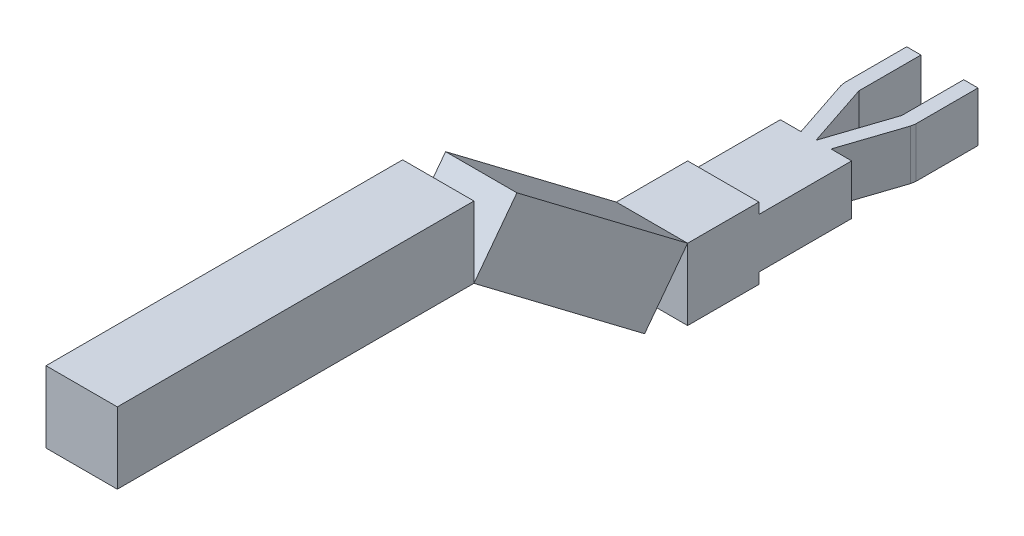
SolidWorks part; units mm, degrees
ref_plane "Front Plane" through (0, 0, 0) normal (0, 0, 1) x (1, 0, 0)
ref_plane "Top Plane" through (0, 0, 0) normal (0, 1, 0) x (1, 0, 0)
ref_plane "Right Plane" through (0, 0, 0) normal (1, 0, 0) x (0, 0, -1)
sketch "Sketch1" plane through (0, 0, 0) normal (0, 1, 0) x (1, 0, 0)
  line L0 (0, -105.7688) -> (-30, -15.63)
  line L1 (-50, 71.37) -> (-30, 71.37)
  line L2 (-50, 71.37) -> (-50, -15.63)
  line L4 (-30, 71.37) -> (-30, -15.63)
  line L5 (30, 71.37) -> (50, 71.37)
  line L6 (30, 71.37) -> (30, -15.63)
  line L8 (50, 71.37) -> (50, -15.63)
  line L9 (21.0786, -105.7688) -> (50, -105.7688)
  line L11 (-21.0786, -105.7688) -> (-48.9766, -21.9458)
  line L12 (0, -105.7688) -> (30, -15.63)
  line L13 (-48.9766, -21.9458) -> (-50, -15.63)
  line L15 (21.0786, -105.7688) -> (48.9766, -21.9458)
  line L16 (-30, 0) -> (0, 0) construction
  line L17 (0, 0) -> (30, 0) construction
  line L18 (50, -15.63) -> (48.9766, -21.9458)
  line L19 (-50, -105.7688) -> (-21.0786, -105.7688)
  line L20 (-50, -105.7688) -> (-50, -235.7688)
  line L21 (-50, -235.7688) -> (50, -235.7688)
  line L22 (50, -105.7688) -> (50, -235.7688)
  dimension "D1" = 20
  dimension "D2" = 20
  dimension "D3" = 60
  dimension "D4" = 87
  dimension "D5" = 95
  dimension "D6" = 100
  dimension "D7" = 130
  dimension "D8" = 20
  dimension "D9" = 20
extrude "Boss-Extrude1" add sketch "Sketch1" along normal blind 70
sketch "Sketch2" plane through (0, 0, 235.7688) normal (0, 0, 1) x (1, 0, 0)
  line L0 (0, 70) -> (0, 0) construction
  line L1 (50, 85) -> (-50, 85)
  line L2 (50, 85) -> (50, -15)
  line L3 (50, -15) -> (-50, -15)
  line L4 (-50, 85) -> (-50, -15)
  line L5 (-50, 70) -> (50, 70) construction
  line L6 (-50, 0) -> (50, 0) construction
  line L7 (0, 0) -> (50, 35) construction
  line L8 (50, 70) -> (50, 0) construction
  line L9 (50, 35) -> (-50, 35) construction
  line L10 (-50, 70) -> (-50, 0) construction
  line L11 (50, 70) -> (0, 35) construction
  line L12 (0, 35) -> (-50, 0) construction
  line L13 (0, 85) -> (0, -15) construction
  point P23 (0, 35)
  dimension "D1" = 100
  dimension "D2" = 100
extrude "Boss-Extrude2" add sketch "Sketch2" along normal blind 100
sketch "Sketch3" plane through (-50, 0, 0) normal (-1, 0, 0) x (0, 0, 1)
  line L0 (335.7688, 85) -> (396.0621, 5.2208)
  line L1 (335.7688, 85) -> (575.1064, 265.8799)
  line L2 (396.0621, 5.2208) -> (635.3996, 186.1007)
  line L3 (575.1064, 265.8799) -> (635.3996, 186.1007)
  dimension "D1" = 100
  dimension "D2" = 300
extrude "Boss-Extrude3" add sketch "Sketch3" against normal blind 100 separate body
sketch "Sketch4" plane through (-50, 0, 0) normal (-1, 0, 0) x (0, 0, 1)
  line L0 (635.3996, 186.1007) -> (1135.3996, 186.1007)
  line L1 (635.3996, 186.1007) -> (635.3996, 286.1007)
  line L2 (1135.3996, 186.1007) -> (1135.3996, 286.1007)
  line L3 (635.3996, 286.1007) -> (1135.3996, 286.1007)
  dimension "D1" = 100
  dimension "D2" = 500
extrude "Boss-Extrude4" add sketch "Sketch4" against normal blind 100 separate body
